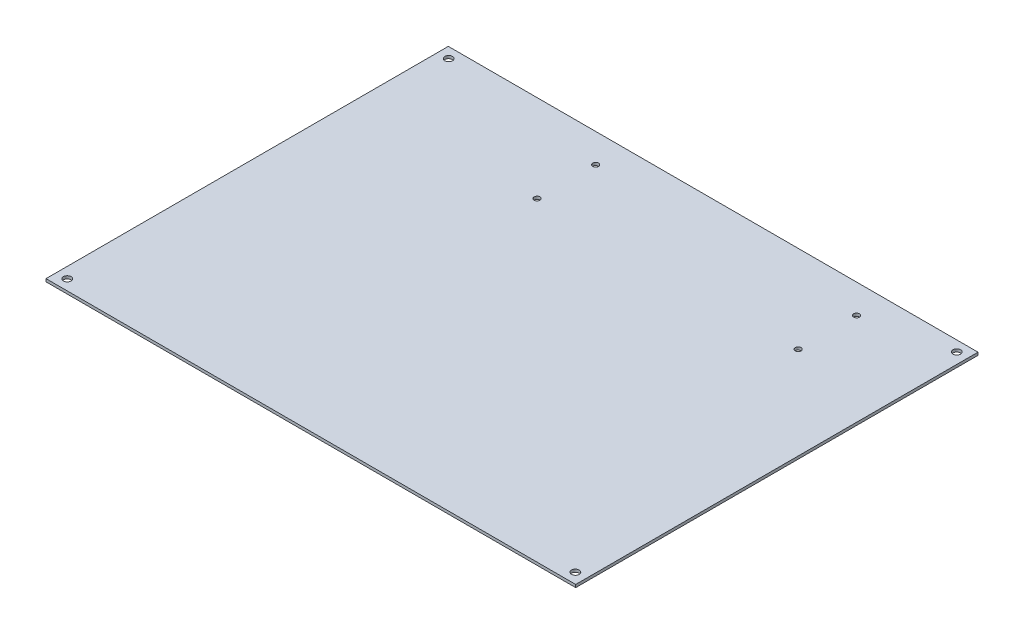
SolidWorks part; units mm, degrees
ref_plane "Front Plane" through (0, 0, 0) normal (0, 0, 1) x (1, 0, 0)
ref_plane "Top Plane" through (0, 0, 0) normal (0, 1, 0) x (1, 0, 0)
ref_plane "Right Plane" through (0, 0, 0) normal (1, 0, 0) x (0, 0, -1)
sketch "Sketch9" plane through (0, 0, 0) normal (0, 1, 0) x (1, 0, 0)
  line L1 (-190.25, 144.5) -> (190.25, 144.5)
  line L2 (-190.25, 144.5) -> (-190.25, -144.5)
  line L3 (-190.25, -144.5) -> (190.25, -144.5)
  line L4 (190.25, 144.5) -> (190.25, -144.5)
extrude "Boss-Extrude2" add sketch "Sketch9" along normal blind 2
sketch "Sketch12" plane through (0, 2, 0) normal (0, 1, 0) x (1, 0, 0)
  point P0 (182.5, 137)
hole_wizard "M5 Clearance Hole1" positions "Sketch13" profile "Sketch14" hole size "M5" standard "ANSI Metric" end condition through all
sketch "Sketch13" plane through (0, 2, 0) normal (0, 1, 0) x (1, 0, 0)
  point P0 (182.5, 137)
sketch "Sketch14" plane through (182.5, 2, -137) normal (1, 0, 0) x (0, 0, 1)
  line L0 (0, 0) -> (0, 2)
  line L1 (0, 2) -> (2.75, 2)
  line L2 (2.75, 2) -> (2.75, 0)
  line L5 (2.75, 0) -> (0, 0)
  line L11 (0, -6.35) -> (0, 107.95) construction
  dimension "Thru Hole Dia." = 5.5
  dimension "Thru Hole Depth" = 2
mirror "Mirror1" about plane through (0, 0, 0) normal (0, 0, 1) of "M5 Clearance Hole1"
mirror "Mirror2" about plane through (0, 0, 0) normal (1, 0, 0) of "Mirror1", "M5 Clearance Hole1"
hole_wizard "Ø4.2 (4.2) Diameter Hole1" positions "Sketch15" profile "Sketch16" hole size "Ø4.2" standard "ANSI Metric" end condition through all
sketch "Sketch15" plane through (0, 2, 0) normal (0, 1, 0) x (1, 0, 0)
  point P0 (-63.6709, 123.7244)
  point P3 (-63.6709, 81.72)
  point P6 (123.8223, 81.7082)
  point P9 (123.8223, 123.7126)
sketch "Sketch16" plane through (-63.6709, 2, -123.7244) normal (1, 0, 0) x (0, 0, 1)
  line L0 (0, 0) -> (0, 2)
  line L1 (0, 2) -> (2.1, 2)
  line L2 (2.1, 2) -> (2.1, 0)
  line L3 (2.1, 0) -> (0, 0)
  line L4 (0, -6.35) -> (0, 107.95) construction
  dimension "Thru Hole Dia." = 4.2
  dimension "Thru Hole Depth" = 2
